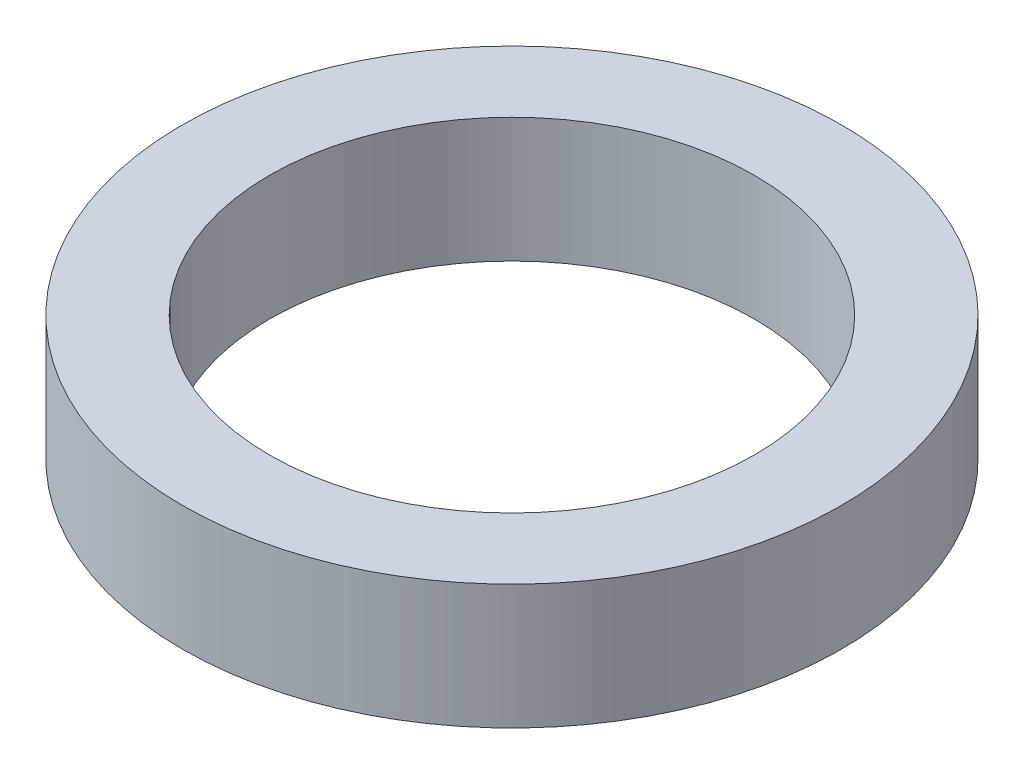
SolidWorks part; units mm, degrees
material "Rubber"
ref_plane "Front Plane" through (0, 0, 0) normal (0, 0, 1) x (1, 0, 0)
ref_plane "Top Plane" through (0, 0, 0) normal (0, 1, 0) x (1, 0, 0)
ref_plane "Right Plane" through (0, 0, 0) normal (1, 0, 0) x (0, 0, -1)
sketch "Sketch1" plane through (0, 0, 0) normal (0, 1, 0) x (1, 0, 0)
  circle A0 centre (0, 0) radius 317.5
  dimension "D1" = 635
extrude "Boss-Extrude1" add sketch "Sketch1" along normal blind 120
sketch "Sketch2" plane through (0, 120, 0) normal (0, 1, 0) x (1, 0, 0)
  circle A0 centre (0, 0) radius 233.5
  circle A2 centre (0, 0) radius 317.5 construction
  dimension "D1" = 84
extrude "Cut-Extrude1" cut sketch "Sketch2" against normal through all
